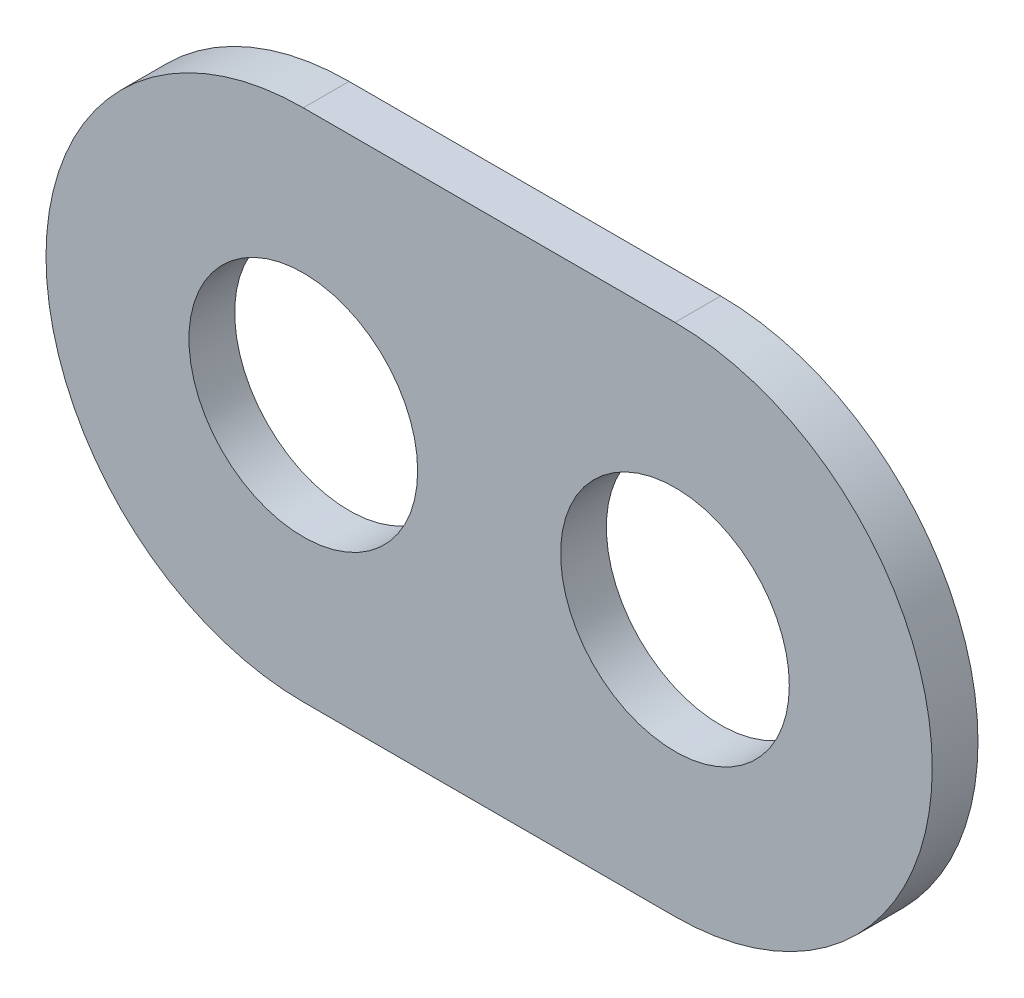
SolidWorks part; units mm, degrees
ref_plane "Front Plane" through (0, 0, 0) normal (0, 0, 1) x (1, 0, 0)
ref_plane "Top Plane" through (0, 0, 0) normal (0, 1, 0) x (1, 0, 0)
ref_plane "Right Plane" through (0, 0, 0) normal (1, 0, 0) x (0, 0, -1)
sketch "Sketch1" plane through (0, 0, 0) normal (0, 0, 1) x (1, 0, 0)
  line L0 (55, 0) -> (-55, 0) construction
  line L1 (0, -55) -> (0, 55) construction
  line L2 (-13, 0) -> (13, 0) construction
  line L3 (-13, 18) -> (13, 18)
  line L4 (-13, -18) -> (13, -18)
  circle A0 centre (-13, 0) radius 8
  arc A1 (-13, 18) -> (-13, -18) centre (-13, 0) ccw
  arc A2 (13, -18) -> (13, 18) centre (13, 0) ccw
  circle A3 centre (13, 0) radius 8
  point P6 (0, 0)
  dimension "D1" = 16
  dimension "D4" = 16
  dimension "D5" = 18
  dimension "D2" = 13
  dimension "D3" = 13
extrude "Boss-Extrude1" add sketch "Sketch1" along normal blind 3.2
